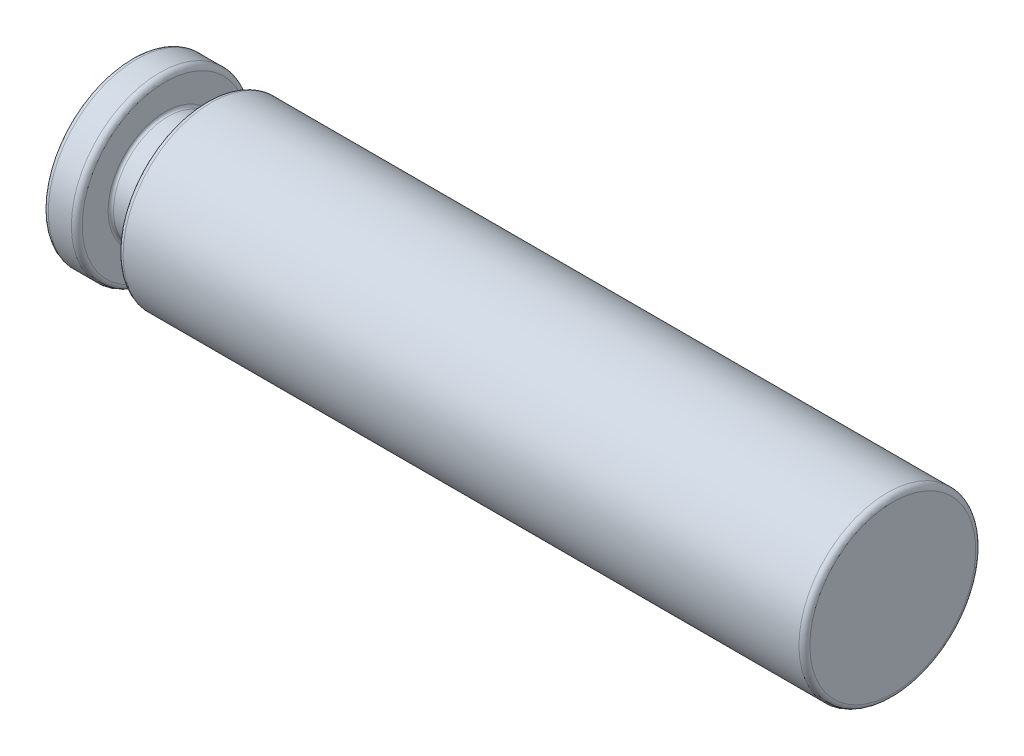
SolidWorks part; units mm, degrees
ref_plane "Plane1" through (0, 0, 0) normal (0, 0, 1) x (1, 0, 0)
ref_plane "Plane2" through (0, 0, 0) normal (0, 1, 0) x (1, 0, 0)
ref_plane "Plane3" through (0, 0, 0) normal (1, 0, 0) x (0, 0, -1)
sketch "Sketch1" plane through (0, 0, 0) normal (0, 0, 1) x (1, 0, 0)
  line L0 (0, 0) -> (112, 0) construction
  line L1 (0, 0) -> (0, 12.2)
  line L2 (0.8, 13) -> (4.2, 13)
  line L3 (5, 12.2) -> (5, 8.4)
  line L4 (5.4, 8) -> (10.6, 8)
  line L5 (11, 8.4) -> (11, 12.2)
  line L6 (11.8, 13) -> (111.2, 13)
  line L7 (112, 12.2) -> (112, 0)
  line L8 (0, 0) -> (112, 0)
  arc A0 (112, 12.2) -> (111.2, 13) centre (111.2, 12.2) ccw
  arc A1 (11.8, 13) -> (11, 12.2) centre (11.8, 12.2) ccw
  arc A2 (0.8, 13) -> (0, 12.2) centre (0.8, 12.2) ccw
  arc A3 (5, 12.2) -> (4.2, 13) centre (4.2, 12.2) ccw
  arc A4 (11, 8.4) -> (10.6, 8) centre (10.6, 8.4) cw
  arc A5 (5.4, 8) -> (5, 8.4) centre (5.4, 8.4) cw
  dimension "D7" = 0.8
  dimension "D8" = 0.4
  dimension "D1" = 26
  dimension "D2" = 16
  dimension "D4" = 101
  dimension "D5" = 6
  dimension "D6" = 112
revolve "Base-Revolve" add sketch "Sketch1" angle 360 about L0
